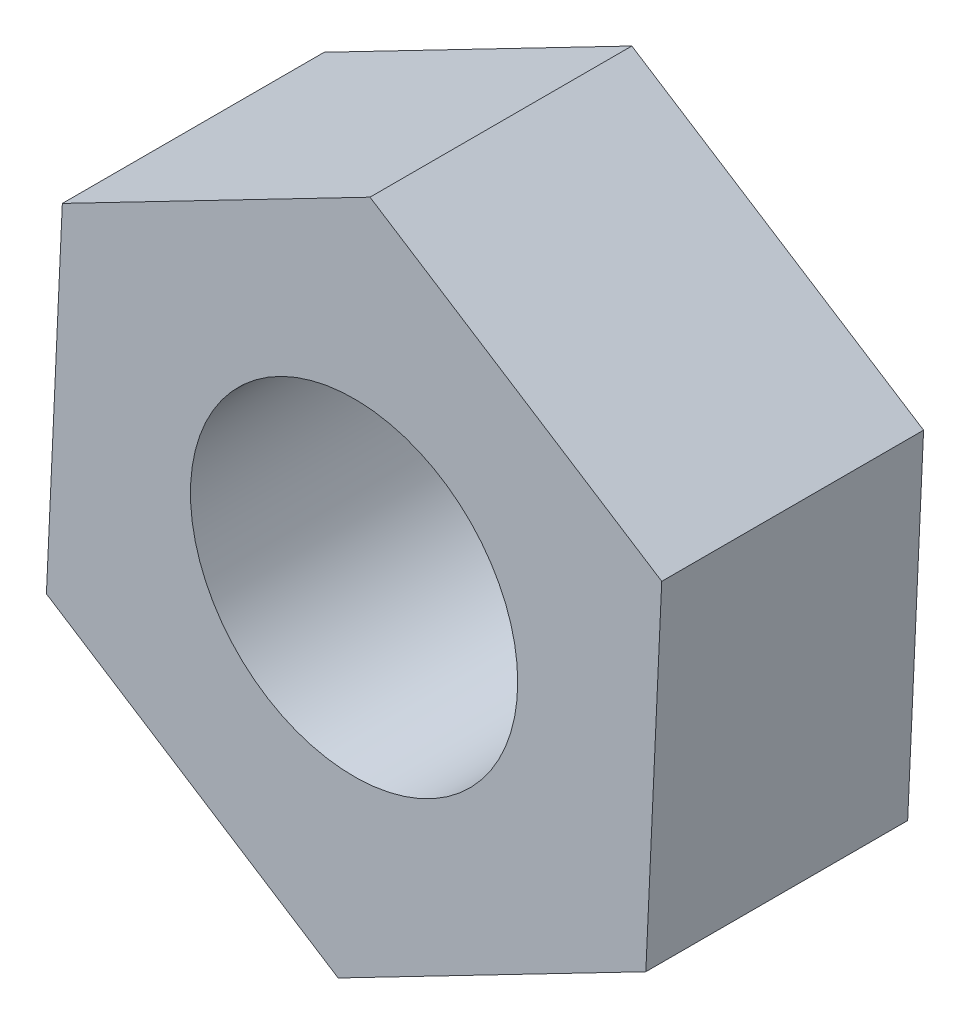
SolidWorks part; units mm, degrees
ref_plane "正面" through (0, 0, 0) normal (0, 0, 1) x (1, 0, 0)
ref_plane "平面" through (0, 0, 0) normal (0, 1, 0) x (1, 0, 0)
ref_plane "右側面" through (0, 0, 0) normal (1, 0, 0) x (0, 0, -1)
sketch "ｽｹｯﾁ1" plane through (0, 0, 0) normal (0, 0, 1) x (1, 0, 0)
  line L1 (-2.8201, -1.4597) -> (-0.1459, -3.1721)
  line L2 (-0.1459, -3.1721) -> (2.6741, -1.7124)
  line L3 (2.6741, -1.7124) -> (2.8201, 1.4597)
  line L4 (2.8201, 1.4597) -> (0.1459, 3.1721)
  line L5 (0.1459, 3.1721) -> (-2.6741, 1.7124)
  line L6 (-2.6741, 1.7124) -> (-2.8201, -1.4597)
  circle A0 centre (0, 0) radius 2.75 construction
  circle A1 centre (0, 0) radius 1.5
  dimension "D2" = 3
  dimension "D1" = 5.5
extrude "ﾎﾞｽ - 押し出し1" add sketch "ｽｹｯﾁ1" along normal blind 2.4
